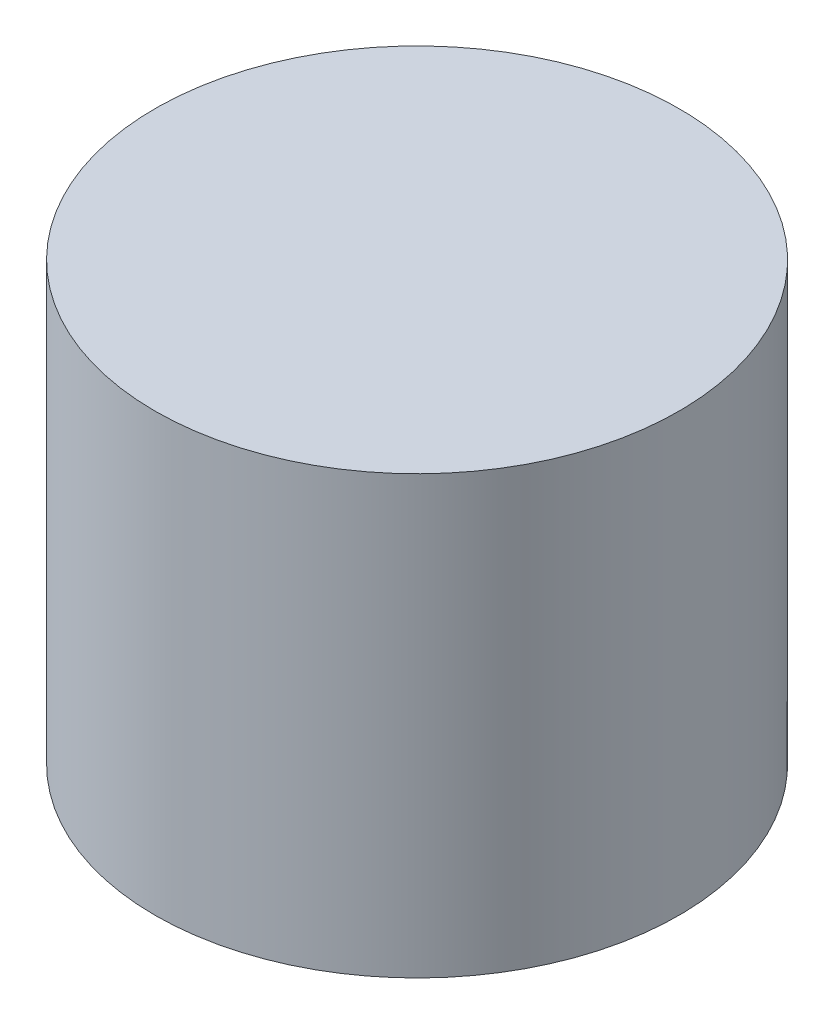
SolidWorks part; units mm, degrees
ref_plane "Front Plane" through (0, 0, 0) normal (0, 0, 1) x (1, 0, 0)
ref_plane "Top Plane" through (0, 0, 0) normal (0, 1, 0) x (1, 0, 0)
ref_plane "Right Plane" through (0, 0, 0) normal (1, 0, 0) x (0, 0, -1)
sketch "Sketch1" plane through (0, 0, 0) normal (0, 1, 0) x (1, 0, 0)
  circle A0 centre (0, 0) radius 6
extrude "Boss-Extrude1" add sketch "Sketch1" along normal blind 10
